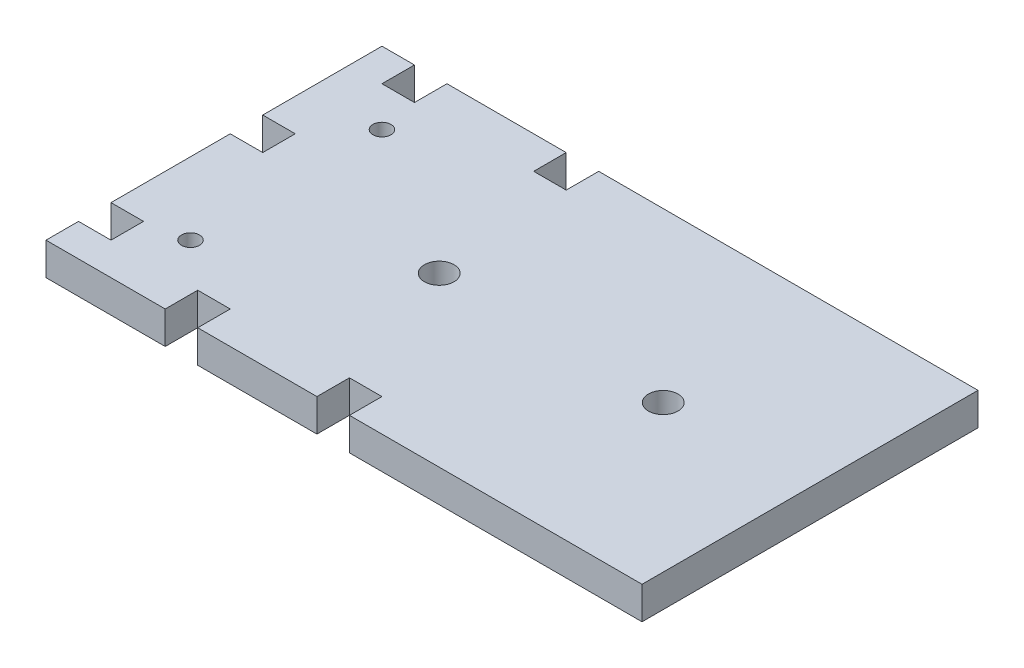
SolidWorks part; units mm, degrees
ref_plane "Front Plane" through (0, 0, 0) normal (0, 0, 1) x (1, 0, 0)
ref_plane "Top Plane" through (0, 0, 0) normal (0, 1, 0) x (1, 0, 0)
ref_plane "Right Plane" through (0, 0, 0) normal (1, 0, 0) x (0, 0, -1)
sketch "Sketch1" plane through (0, 0, 0) normal (0, 1, 0) x (1, 0, 0)
  line L1 (-41.25, 23.25) -> (41.25, 23.25)
  line L2 (-41.25, 23.25) -> (-41.25, -23.25)
  line L3 (-41.25, -23.25) -> (41.25, -23.25)
  line L4 (41.25, 23.25) -> (41.25, -23.25)
  line L5 (-41.25, 23.25) -> (41.25, -23.25) construction
  line L6 (-41.25, -23.25) -> (41.25, 23.25) construction
  circle A0 centre (20.9292, 0) radius 2.05
  circle A1 centre (-10.0708, 0) radius 2.05
  point P0 (0, 0)
  dimension "D3" = 31
  dimension "D5" = 4.1
  dimension "D6" = 4.1
  dimension "D1" = 82.5
  dimension "D2" = 46.5
  dimension "D4" = 31.1792
extrude "Boss-Extrude1" add sketch "Sketch1" along normal blind 4.5
sketch "Sketch2" plane through (0, 4.5, 0) normal (0, 1, 0) x (1, 0, 0)
  line L0 (41.25, 23.25) -> (-41.25, 23.25) construction
  line L1 (-41.25, 23.25) -> (-41.25, -23.25) construction
  line L3 (-41.25, -23.25) -> (41.25, -23.25) construction
  circle A0 centre (-31.25, -13.25) radius 1.25
  circle A1 centre (-31.25, 13.25) radius 1.25
  dimension "D2" = 10
  dimension "D4" = 2.5
  dimension "D5" = 2.5
  dimension "D11" = 10
  dimension "D3" = 10
extrude "Cut-Extrude1" cut sketch "Sketch2" against normal through all
sketch "Sketch3" plane through (0, 0, 0) normal (0, -1, 0) x (-1, 0, 0)
  line L0 (-41.25, 23.25) -> (41.25, 23.25) construction
  line L1 (36.75, 23.25) -> (32.25, 23.25)
  line L2 (36.75, 23.25) -> (36.75, 18.75)
  line L3 (36.75, 18.75) -> (32.25, 18.75)
  line L4 (32.25, 23.25) -> (32.25, 18.75)
  line L5 (41.25, 23.25) -> (41.25, -23.25) construction
  line L6 (41.25, 6.75) -> (36.75, 6.75)
  line L7 (41.25, 6.75) -> (41.25, 2.25)
  line L8 (41.25, 2.25) -> (36.75, 2.25)
  line L9 (36.75, 6.75) -> (36.75, 2.25)
  line L10 (41.25, -23.25) -> (-41.25, -23.25) construction
  line L11 (41.25, -14.25) -> (36.75, -14.25)
  line L12 (41.25, -14.25) -> (41.25, -18.75)
  line L13 (41.25, -18.75) -> (36.75, -18.75)
  line L14 (36.75, -14.25) -> (36.75, -18.75)
  line L15 (24.75, -23.25) -> (20.25, -23.25)
  line L16 (24.75, -23.25) -> (24.75, -18.75)
  line L17 (24.75, -18.75) -> (20.25, -18.75)
  line L18 (20.25, -23.25) -> (20.25, -18.75)
  line L20 (3.75, -23.25) -> (-0.75, -23.25)
  line L21 (3.75, -23.25) -> (3.75, -18.75)
  line L22 (3.75, -18.75) -> (-0.75, -18.75)
  line L23 (-0.75, -23.25) -> (-0.75, -18.75)
  line L24 (15.75, 23.25) -> (11.25, 23.25)
  line L25 (15.75, 23.25) -> (15.75, 18.75)
  line L26 (15.75, 18.75) -> (11.25, 18.75)
  line L27 (11.25, 23.25) -> (11.25, 18.75)
  dimension "D1" = 4.5
  dimension "D2" = 4.5
  dimension "D3" = 4.5
  dimension "D4" = 16.5
  dimension "D5" = 4.5
  dimension "D6" = 4.5
  dimension "D7" = 4.5
  dimension "D8" = 4.5
  dimension "D9" = 4.5
  dimension "D10" = 16.5
  dimension "D11" = 4.5
  dimension "D12" = 4.5
  dimension "D13" = 16.5
  dimension "D14" = 4.5
  dimension "D15" = 4.5
  dimension "D16" = 16.5
  dimension "D17" = 4.5
  dimension "D18" = 4.5
extrude "Cut-Extrude2" cut sketch "Sketch3" against normal through all
sketch "Sketch6" plane through (0, 4.5, 0) normal (0, 1, 0) x (1, 0, 0)
